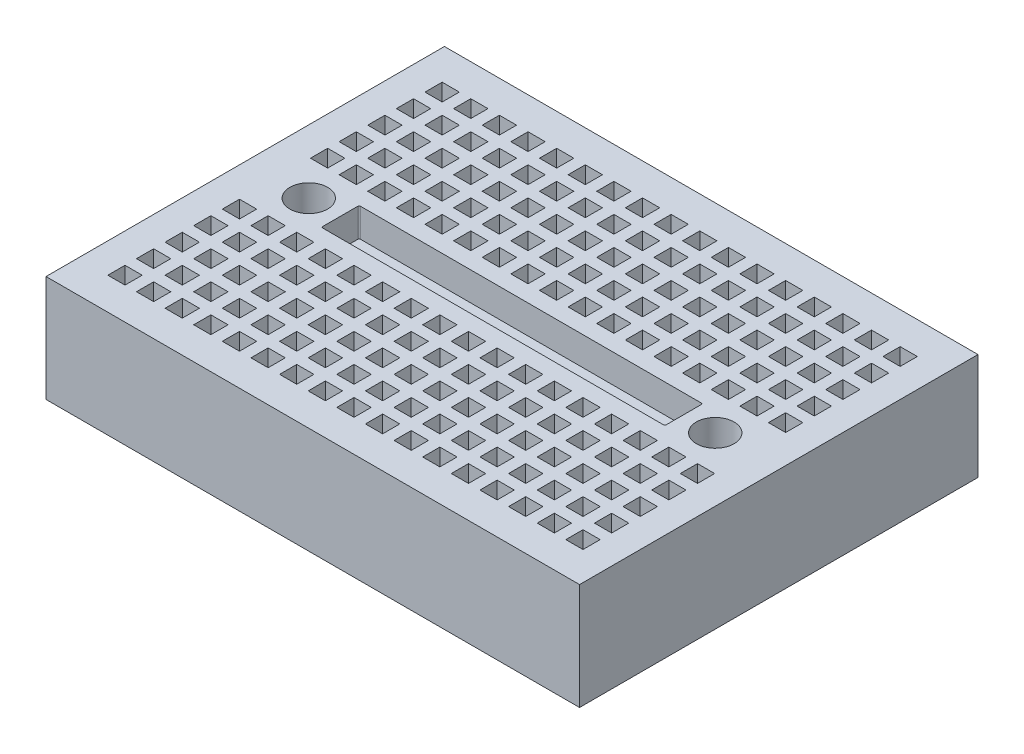
SolidWorks part; units mm, degrees
material "ABS"
ref_plane "Alzado" through (0, 0, 0) normal (0, 0, 1) x (1, 0, 0)
ref_plane "Planta" through (0, 0, 0) normal (0, 1, 0) x (1, 0, 0)
ref_plane "Vista lateral" through (0, 0, 0) normal (1, 0, 0) x (0, 0, -1)
sketch "Croquis2" plane through (0, 0, 0) normal (0, 1, 0) x (1, 0, 0)
  line L1 (-23.3, -17.4) -> (23.3, -17.4)
  line L2 (-23.3, -17.4) -> (-23.3, 17.4)
  line L3 (-23.3, 17.4) -> (23.3, 17.4)
  line L4 (23.3, -17.4) -> (23.3, 17.4)
  line L5 (-23.3, -17.4) -> (23.3, 17.4) construction
  line L6 (-23.3, 17.4) -> (23.3, -17.4) construction
  point P0 (0, 0)
  dimension "D1" = 34.8
  dimension "D2" = 46.6
extrude "Saliente-Extruir1" add sketch "Croquis2" along normal blind 9.3
sketch "Croquis3" plane through (0, 9.3, 0) normal (0, 1, 0) x (1, 0, 0)
  line L0 (23.3, -17.4) -> (23.3, 17.4) construction
  line L1 (20.8, -14.6) -> (19.3, -14.6)
  line L2 (20.8, -14.6) -> (20.8, -13.1)
  line L3 (20.8, -13.1) -> (19.3, -13.1)
  line L4 (19.3, -14.6) -> (19.3, -13.1)
  line L5 (-23.3, -17.4) -> (23.3, -17.4) construction
  line L6 (18.3, -14.6) -> (18.3, -13.1)
  line L7 (18.3, -14.6) -> (16.8, -14.6)
  line L8 (16.8, -14.6) -> (16.8, -13.1)
  line L9 (18.3, -13.1) -> (16.8, -13.1)
  line L10 (15.8, -14.6) -> (15.8, -13.1)
  line L11 (15.8, -14.6) -> (14.3, -14.6)
  line L12 (14.3, -14.6) -> (14.3, -13.1)
  line L13 (15.8, -13.1) -> (14.3, -13.1)
  line L14 (13.3, -14.6) -> (13.3, -13.1)
  line L15 (13.3, -14.6) -> (11.8, -14.6)
  line L16 (11.8, -14.6) -> (11.8, -13.1)
  line L17 (13.3, -13.1) -> (11.8, -13.1)
  line L18 (10.8, -14.6) -> (10.8, -13.1)
  line L19 (10.8, -14.6) -> (9.3, -14.6)
  line L20 (9.3, -14.6) -> (9.3, -13.1)
  line L21 (10.8, -13.1) -> (9.3, -13.1)
  line L22 (8.3, -14.6) -> (8.3, -13.1)
  line L23 (8.3, -14.6) -> (6.8, -14.6)
  line L24 (6.8, -14.6) -> (6.8, -13.1)
  line L25 (8.3, -13.1) -> (6.8, -13.1)
  line L26 (5.8, -14.6) -> (5.8, -13.1)
  line L27 (5.8, -14.6) -> (4.3, -14.6)
  line L28 (4.3, -14.6) -> (4.3, -13.1)
  line L29 (5.8, -13.1) -> (4.3, -13.1)
  line L30 (3.3, -14.6) -> (3.3, -13.1)
  line L31 (3.3, -14.6) -> (1.8, -14.6)
  line L32 (1.8, -14.6) -> (1.8, -13.1)
  line L33 (3.3, -13.1) -> (1.8, -13.1)
  line L34 (0.8, -14.6) -> (0.8, -13.1)
  line L35 (0.8, -14.6) -> (-0.7, -14.6)
  line L36 (-0.7, -14.6) -> (-0.7, -13.1)
  line L37 (0.8, -13.1) -> (-0.7, -13.1)
  line L38 (-1.7, -14.6) -> (-1.7, -13.1)
  line L39 (-1.7, -14.6) -> (-3.2, -14.6)
  line L40 (-3.2, -14.6) -> (-3.2, -13.1)
  line L41 (-1.7, -13.1) -> (-3.2, -13.1)
  line L42 (-4.2, -14.6) -> (-4.2, -13.1)
  line L43 (-4.2, -14.6) -> (-5.7, -14.6)
  line L44 (-5.7, -14.6) -> (-5.7, -13.1)
  line L45 (-4.2, -13.1) -> (-5.7, -13.1)
  line L46 (-6.7, -14.6) -> (-6.7, -13.1)
  line L47 (-6.7, -14.6) -> (-8.2, -14.6)
  line L48 (-8.2, -14.6) -> (-8.2, -13.1)
  line L49 (-6.7, -13.1) -> (-8.2, -13.1)
  line L50 (-9.2, -14.6) -> (-9.2, -13.1)
  line L51 (-9.2, -14.6) -> (-10.7, -14.6)
  line L52 (-10.7, -14.6) -> (-10.7, -13.1)
  line L53 (-9.2, -13.1) -> (-10.7, -13.1)
  line L54 (-11.7, -14.6) -> (-11.7, -13.1)
  line L55 (-11.7, -14.6) -> (-13.2, -14.6)
  line L56 (-13.2, -14.6) -> (-13.2, -13.1)
  line L57 (-11.7, -13.1) -> (-13.2, -13.1)
  line L58 (-14.2, -14.6) -> (-14.2, -13.1)
  line L59 (-14.2, -14.6) -> (-15.7, -14.6)
  line L60 (-15.7, -14.6) -> (-15.7, -13.1)
  line L61 (-14.2, -13.1) -> (-15.7, -13.1)
  line L62 (-16.7, -14.6) -> (-16.7, -13.1)
  line L63 (-16.7, -14.6) -> (-18.2, -14.6)
  line L64 (-18.2, -14.6) -> (-18.2, -13.1)
  line L65 (-16.7, -13.1) -> (-18.2, -13.1)
  line L66 (-19.2, -14.6) -> (-19.2, -13.1)
  line L67 (-19.2, -14.6) -> (-20.7, -14.6)
  line L68 (-20.7, -14.6) -> (-20.7, -13.1)
  line L69 (-19.2, -13.1) -> (-20.7, -13.1)
  line L70 (-19.2, -12.1) -> (-19.2, -10.6)
  line L71 (-19.2, -10.6) -> (-20.7, -10.6)
  line L72 (-20.7, -12.1) -> (-20.7, -10.6)
  line L73 (-19.2, -12.1) -> (-20.7, -12.1)
  line L74 (-16.7, -12.1) -> (-16.7, -10.6)
  line L75 (-16.7, -10.6) -> (-18.2, -10.6)
  line L76 (-18.2, -12.1) -> (-18.2, -10.6)
  line L77 (-16.7, -12.1) -> (-18.2, -12.1)
  line L78 (-14.2, -12.1) -> (-14.2, -10.6)
  line L79 (-14.2, -10.6) -> (-15.7, -10.6)
  line L80 (-15.7, -12.1) -> (-15.7, -10.6)
  line L81 (-14.2, -12.1) -> (-15.7, -12.1)
  line L82 (-11.7, -12.1) -> (-11.7, -10.6)
  line L83 (-11.7, -10.6) -> (-13.2, -10.6)
  line L84 (-13.2, -12.1) -> (-13.2, -10.6)
  line L85 (-11.7, -12.1) -> (-13.2, -12.1)
  line L86 (3.3, -12.1) -> (3.3, -10.6)
  line L87 (3.3, -10.6) -> (1.8, -10.6)
  line L88 (1.8, -12.1) -> (1.8, -10.6)
  line L89 (3.3, -12.1) -> (1.8, -12.1)
  line L90 (0.8, -12.1) -> (0.8, -10.6)
  line L91 (0.8, -10.6) -> (-0.7, -10.6)
  line L92 (-0.7, -12.1) -> (-0.7, -10.6)
  line L93 (0.8, -12.1) -> (-0.7, -12.1)
  line L94 (-1.7, -12.1) -> (-1.7, -10.6)
  line L95 (-1.7, -10.6) -> (-3.2, -10.6)
  line L96 (-3.2, -12.1) -> (-3.2, -10.6)
  line L97 (-1.7, -12.1) -> (-3.2, -12.1)
  line L98 (-4.2, -12.1) -> (-4.2, -10.6)
  line L99 (-4.2, -10.6) -> (-5.7, -10.6)
  line L100 (-5.7, -12.1) -> (-5.7, -10.6)
  line L101 (-4.2, -12.1) -> (-5.7, -12.1)
  line L102 (-9.2, -12.1) -> (-9.2, -10.6)
  line L103 (-9.2, -10.6) -> (-10.7, -10.6)
  line L104 (-10.7, -12.1) -> (-10.7, -10.6)
  line L105 (-9.2, -12.1) -> (-10.7, -12.1)
  line L106 (-6.7, -12.1) -> (-6.7, -10.6)
  line L107 (-6.7, -10.6) -> (-8.2, -10.6)
  line L108 (-8.2, -12.1) -> (-8.2, -10.6)
  line L109 (-6.7, -12.1) -> (-8.2, -12.1)
  line L110 (5.8, -12.1) -> (5.8, -10.6)
  line L111 (5.8, -10.6) -> (4.3, -10.6)
  line L112 (4.3, -12.1) -> (4.3, -10.6)
  line L113 (5.8, -12.1) -> (4.3, -12.1)
  line L114 (8.3, -12.1) -> (8.3, -10.6)
  line L115 (8.3, -10.6) -> (6.8, -10.6)
  line L116 (6.8, -12.1) -> (6.8, -10.6)
  line L117 (8.3, -12.1) -> (6.8, -12.1)
  line L118 (10.8, -12.1) -> (10.8, -10.6)
  line L119 (10.8, -10.6) -> (9.3, -10.6)
  line L120 (9.3, -12.1) -> (9.3, -10.6)
  line L121 (10.8, -12.1) -> (9.3, -12.1)
  line L122 (13.3, -12.1) -> (13.3, -10.6)
  line L123 (13.3, -10.6) -> (11.8, -10.6)
  line L124 (11.8, -12.1) -> (11.8, -10.6)
  line L125 (13.3, -12.1) -> (11.8, -12.1)
  line L126 (15.8, -12.1) -> (15.8, -10.6)
  line L127 (15.8, -10.6) -> (14.3, -10.6)
  line L128 (14.3, -12.1) -> (14.3, -10.6)
  line L129 (15.8, -12.1) -> (14.3, -12.1)
  line L130 (18.3, -12.1) -> (18.3, -10.6)
  line L131 (18.3, -10.6) -> (16.8, -10.6)
  line L132 (16.8, -12.1) -> (16.8, -10.6)
  line L133 (18.3, -12.1) -> (16.8, -12.1)
  line L134 (20.8, -12.1) -> (20.8, -10.6)
  line L135 (20.8, -12.1) -> (19.3, -12.1)
  line L136 (19.3, -12.1) -> (19.3, -10.6)
  line L137 (20.8, -10.6) -> (19.3, -10.6)
  line L138 (-19.2, -9.6) -> (-19.2, -8.1)
  line L139 (-19.2, -8.1) -> (-20.7, -8.1)
  line L140 (-20.7, -9.6) -> (-20.7, -8.1)
  line L141 (-19.2, -9.6) -> (-20.7, -9.6)
  line L142 (-16.7, -9.6) -> (-16.7, -8.1)
  line L143 (-16.7, -8.1) -> (-18.2, -8.1)
  line L144 (-18.2, -9.6) -> (-18.2, -8.1)
  line L145 (-16.7, -9.6) -> (-18.2, -9.6)
  line L146 (-14.2, -9.6) -> (-14.2, -8.1)
  line L147 (-14.2, -8.1) -> (-15.7, -8.1)
  line L148 (-15.7, -9.6) -> (-15.7, -8.1)
  line L149 (-14.2, -9.6) -> (-15.7, -9.6)
  line L150 (-11.7, -9.6) -> (-11.7, -8.1)
  line L151 (-11.7, -8.1) -> (-13.2, -8.1)
  line L152 (-13.2, -9.6) -> (-13.2, -8.1)
  line L153 (-11.7, -9.6) -> (-13.2, -9.6)
  line L154 (3.3, -9.6) -> (3.3, -8.1)
  line L155 (3.3, -8.1) -> (1.8, -8.1)
  line L156 (1.8, -9.6) -> (1.8, -8.1)
  line L157 (3.3, -9.6) -> (1.8, -9.6)
  line L158 (0.8, -9.6) -> (0.8, -8.1)
  line L159 (0.8, -8.1) -> (-0.7, -8.1)
  line L160 (-0.7, -9.6) -> (-0.7, -8.1)
  line L161 (0.8, -9.6) -> (-0.7, -9.6)
  line L162 (-1.7, -9.6) -> (-1.7, -8.1)
  line L163 (-1.7, -8.1) -> (-3.2, -8.1)
  line L164 (-3.2, -9.6) -> (-3.2, -8.1)
  line L165 (-1.7, -9.6) -> (-3.2, -9.6)
  line L166 (-4.2, -9.6) -> (-4.2, -8.1)
  line L167 (-4.2, -8.1) -> (-5.7, -8.1)
  line L168 (-5.7, -9.6) -> (-5.7, -8.1)
  line L169 (-4.2, -9.6) -> (-5.7, -9.6)
  line L170 (-9.2, -9.6) -> (-9.2, -8.1)
  line L171 (-9.2, -8.1) -> (-10.7, -8.1)
  line L172 (-10.7, -9.6) -> (-10.7, -8.1)
  line L173 (-9.2, -9.6) -> (-10.7, -9.6)
  line L174 (-6.7, -9.6) -> (-6.7, -8.1)
  line L175 (-6.7, -8.1) -> (-8.2, -8.1)
  line L176 (-8.2, -9.6) -> (-8.2, -8.1)
  line L177 (-6.7, -9.6) -> (-8.2, -9.6)
  line L178 (5.8, -9.6) -> (5.8, -8.1)
  line L179 (5.8, -8.1) -> (4.3, -8.1)
  line L180 (4.3, -9.6) -> (4.3, -8.1)
  line L181 (5.8, -9.6) -> (4.3, -9.6)
  line L182 (8.3, -9.6) -> (8.3, -8.1)
  line L183 (8.3, -8.1) -> (6.8, -8.1)
  line L184 (6.8, -9.6) -> (6.8, -8.1)
  line L185 (8.3, -9.6) -> (6.8, -9.6)
  line L186 (10.8, -9.6) -> (10.8, -8.1)
  line L187 (10.8, -8.1) -> (9.3, -8.1)
  line L188 (9.3, -9.6) -> (9.3, -8.1)
  line L189 (10.8, -9.6) -> (9.3, -9.6)
  line L190 (13.3, -9.6) -> (13.3, -8.1)
  line L191 (13.3, -8.1) -> (11.8, -8.1)
  line L192 (11.8, -9.6) -> (11.8, -8.1)
  line L193 (13.3, -9.6) -> (11.8, -9.6)
  line L194 (15.8, -9.6) -> (15.8, -8.1)
  line L195 (15.8, -8.1) -> (14.3, -8.1)
  line L196 (14.3, -9.6) -> (14.3, -8.1)
  line L197 (15.8, -9.6) -> (14.3, -9.6)
  line L198 (18.3, -9.6) -> (18.3, -8.1)
  line L199 (18.3, -8.1) -> (16.8, -8.1)
  line L200 (16.8, -9.6) -> (16.8, -8.1)
  line L201 (18.3, -9.6) -> (16.8, -9.6)
  line L202 (20.8, -9.6) -> (20.8, -8.1)
  line L203 (20.8, -9.6) -> (19.3, -9.6)
  line L204 (19.3, -9.6) -> (19.3, -8.1)
  line L205 (20.8, -8.1) -> (19.3, -8.1)
  line L206 (-19.2, -7.1) -> (-19.2, -5.6)
  line L207 (-19.2, -5.6) -> (-20.7, -5.6)
  line L208 (-20.7, -7.1) -> (-20.7, -5.6)
  line L209 (-19.2, -7.1) -> (-20.7, -7.1)
  line L210 (-16.7, -7.1) -> (-16.7, -5.6)
  line L211 (-16.7, -5.6) -> (-18.2, -5.6)
  line L212 (-18.2, -7.1) -> (-18.2, -5.6)
  line L213 (-16.7, -7.1) -> (-18.2, -7.1)
  line L214 (-14.2, -7.1) -> (-14.2, -5.6)
  line L215 (-14.2, -5.6) -> (-15.7, -5.6)
  line L216 (-15.7, -7.1) -> (-15.7, -5.6)
  line L217 (-14.2, -7.1) -> (-15.7, -7.1)
  line L218 (-11.7, -7.1) -> (-11.7, -5.6)
  line L219 (-11.7, -5.6) -> (-13.2, -5.6)
  line L220 (-13.2, -7.1) -> (-13.2, -5.6)
  line L221 (-11.7, -7.1) -> (-13.2, -7.1)
  line L222 (3.3, -7.1) -> (3.3, -5.6)
  line L223 (3.3, -5.6) -> (1.8, -5.6)
  line L224 (1.8, -7.1) -> (1.8, -5.6)
  line L225 (3.3, -7.1) -> (1.8, -7.1)
  line L226 (0.8, -7.1) -> (0.8, -5.6)
  line L227 (0.8, -5.6) -> (-0.7, -5.6)
  line L228 (-0.7, -7.1) -> (-0.7, -5.6)
  line L229 (0.8, -7.1) -> (-0.7, -7.1)
  line L230 (-1.7, -7.1) -> (-1.7, -5.6)
  line L231 (-1.7, -5.6) -> (-3.2, -5.6)
  line L232 (-3.2, -7.1) -> (-3.2, -5.6)
  line L233 (-1.7, -7.1) -> (-3.2, -7.1)
  line L234 (-4.2, -7.1) -> (-4.2, -5.6)
  line L235 (-4.2, -5.6) -> (-5.7, -5.6)
  line L236 (-5.7, -7.1) -> (-5.7, -5.6)
  line L237 (-4.2, -7.1) -> (-5.7, -7.1)
  line L238 (-9.2, -7.1) -> (-9.2, -5.6)
  line L239 (-9.2, -5.6) -> (-10.7, -5.6)
  line L240 (-10.7, -7.1) -> (-10.7, -5.6)
  line L241 (-9.2, -7.1) -> (-10.7, -7.1)
  line L242 (-6.7, -7.1) -> (-6.7, -5.6)
  line L243 (-6.7, -5.6) -> (-8.2, -5.6)
  line L244 (-8.2, -7.1) -> (-8.2, -5.6)
  line L245 (-6.7, -7.1) -> (-8.2, -7.1)
  line L246 (5.8, -7.1) -> (5.8, -5.6)
  line L247 (5.8, -5.6) -> (4.3, -5.6)
  line L248 (4.3, -7.1) -> (4.3, -5.6)
  line L249 (5.8, -7.1) -> (4.3, -7.1)
  line L250 (8.3, -7.1) -> (8.3, -5.6)
  line L251 (8.3, -5.6) -> (6.8, -5.6)
  line L252 (6.8, -7.1) -> (6.8, -5.6)
  line L253 (8.3, -7.1) -> (6.8, -7.1)
  line L254 (10.8, -7.1) -> (10.8, -5.6)
  line L255 (10.8, -5.6) -> (9.3, -5.6)
  line L256 (9.3, -7.1) -> (9.3, -5.6)
  line L257 (10.8, -7.1) -> (9.3, -7.1)
  line L258 (13.3, -7.1) -> (13.3, -5.6)
  line L259 (13.3, -5.6) -> (11.8, -5.6)
  line L260 (11.8, -7.1) -> (11.8, -5.6)
  line L261 (13.3, -7.1) -> (11.8, -7.1)
  line L262 (15.8, -7.1) -> (15.8, -5.6)
  line L263 (15.8, -5.6) -> (14.3, -5.6)
  line L264 (14.3, -7.1) -> (14.3, -5.6)
  line L265 (15.8, -7.1) -> (14.3, -7.1)
  line L266 (18.3, -7.1) -> (18.3, -5.6)
  line L267 (18.3, -5.6) -> (16.8, -5.6)
  line L268 (16.8, -7.1) -> (16.8, -5.6)
  line L269 (18.3, -7.1) -> (16.8, -7.1)
  line L270 (20.8, -7.1) -> (20.8, -5.6)
  line L271 (20.8, -7.1) -> (19.3, -7.1)
  line L272 (19.3, -7.1) -> (19.3, -5.6)
  line L273 (20.8, -5.6) -> (19.3, -5.6)
  line L274 (-19.2, -4.6) -> (-19.2, -3.1)
  line L275 (-19.2, -3.1) -> (-20.7, -3.1)
  line L276 (-20.7, -4.6) -> (-20.7, -3.1)
  line L277 (-19.2, -4.6) -> (-20.7, -4.6)
  line L278 (-16.7, -4.6) -> (-16.7, -3.1)
  line L279 (-16.7, -3.1) -> (-18.2, -3.1)
  line L280 (-18.2, -4.6) -> (-18.2, -3.1)
  line L281 (-16.7, -4.6) -> (-18.2, -4.6)
  line L282 (-14.2, -4.6) -> (-14.2, -3.1)
  line L283 (-14.2, -3.1) -> (-15.7, -3.1)
  line L284 (-15.7, -4.6) -> (-15.7, -3.1)
  line L285 (-14.2, -4.6) -> (-15.7, -4.6)
  line L286 (-11.7, -4.6) -> (-11.7, -3.1)
  line L287 (-11.7, -3.1) -> (-13.2, -3.1)
  line L288 (-13.2, -4.6) -> (-13.2, -3.1)
  line L289 (-11.7, -4.6) -> (-13.2, -4.6)
  line L290 (3.3, -4.6) -> (3.3, -3.1)
  line L291 (3.3, -3.1) -> (1.8, -3.1)
  line L292 (1.8, -4.6) -> (1.8, -3.1)
  line L293 (3.3, -4.6) -> (1.8, -4.6)
  line L294 (0.8, -4.6) -> (0.8, -3.1)
  line L295 (0.8, -3.1) -> (-0.7, -3.1)
  line L296 (-0.7, -4.6) -> (-0.7, -3.1)
  line L297 (0.8, -4.6) -> (-0.7, -4.6)
  line L298 (-1.7, -4.6) -> (-1.7, -3.1)
  line L299 (-1.7, -3.1) -> (-3.2, -3.1)
  line L300 (-3.2, -4.6) -> (-3.2, -3.1)
  line L301 (-1.7, -4.6) -> (-3.2, -4.6)
  line L302 (-4.2, -4.6) -> (-4.2, -3.1)
  line L303 (-4.2, -3.1) -> (-5.7, -3.1)
  line L304 (-5.7, -4.6) -> (-5.7, -3.1)
  line L305 (-4.2, -4.6) -> (-5.7, -4.6)
  line L306 (-9.2, -4.6) -> (-9.2, -3.1)
  line L307 (-9.2, -3.1) -> (-10.7, -3.1)
  line L308 (-10.7, -4.6) -> (-10.7, -3.1)
  line L309 (-9.2, -4.6) -> (-10.7, -4.6)
  line L310 (-6.7, -4.6) -> (-6.7, -3.1)
  line L311 (-6.7, -3.1) -> (-8.2, -3.1)
  line L312 (-8.2, -4.6) -> (-8.2, -3.1)
  line L313 (-6.7, -4.6) -> (-8.2, -4.6)
  line L314 (5.8, -4.6) -> (5.8, -3.1)
  line L315 (5.8, -3.1) -> (4.3, -3.1)
  line L316 (4.3, -4.6) -> (4.3, -3.1)
  line L317 (5.8, -4.6) -> (4.3, -4.6)
  line L318 (8.3, -4.6) -> (8.3, -3.1)
  line L319 (8.3, -3.1) -> (6.8, -3.1)
  line L320 (6.8, -4.6) -> (6.8, -3.1)
  line L321 (8.3, -4.6) -> (6.8, -4.6)
  line L322 (10.8, -4.6) -> (10.8, -3.1)
  line L323 (10.8, -3.1) -> (9.3, -3.1)
  line L324 (9.3, -4.6) -> (9.3, -3.1)
  line L325 (10.8, -4.6) -> (9.3, -4.6)
  line L326 (13.3, -4.6) -> (13.3, -3.1)
  line L327 (13.3, -3.1) -> (11.8, -3.1)
  line L328 (11.8, -4.6) -> (11.8, -3.1)
  line L329 (13.3, -4.6) -> (11.8, -4.6)
  line L330 (15.8, -4.6) -> (15.8, -3.1)
  line L331 (15.8, -3.1) -> (14.3, -3.1)
  line L332 (14.3, -4.6) -> (14.3, -3.1)
  line L333 (15.8, -4.6) -> (14.3, -4.6)
  line L334 (18.3, -4.6) -> (18.3, -3.1)
  line L335 (18.3, -3.1) -> (16.8, -3.1)
  line L336 (16.8, -4.6) -> (16.8, -3.1)
  line L337 (18.3, -4.6) -> (16.8, -4.6)
  line L338 (20.8, -4.6) -> (20.8, -3.1)
  line L339 (20.8, -4.6) -> (19.3, -4.6)
  line L340 (19.3, -4.6) -> (19.3, -3.1)
  line L341 (20.8, -3.1) -> (19.3, -3.1)
  line L342 (-19.2, -14.6) -> (-19.2, -12.1) construction
  line L343 (-23.3, 0) -> (23.3, 0) construction
  line L344 (-23.3, 17.4) -> (-23.3, -17.4) construction
  line L345 (-19.2, 14.6) -> (-19.2, 12.1) construction
  line L346 (20.8, 3.1) -> (19.3, 3.1)
  line L347 (19.3, 4.6) -> (19.3, 3.1)
  line L348 (20.8, 4.6) -> (19.3, 4.6)
  line L349 (20.8, 4.6) -> (20.8, 3.1)
  line L350 (18.3, 4.6) -> (16.8, 4.6)
  line L351 (16.8, 4.6) -> (16.8, 3.1)
  line L352 (18.3, 3.1) -> (16.8, 3.1)
  line L353 (18.3, 4.6) -> (18.3, 3.1)
  line L354 (15.8, 4.6) -> (14.3, 4.6)
  line L355 (14.3, 4.6) -> (14.3, 3.1)
  line L356 (15.8, 3.1) -> (14.3, 3.1)
  line L357 (15.8, 4.6) -> (15.8, 3.1)
  line L358 (13.3, 4.6) -> (11.8, 4.6)
  line L359 (11.8, 4.6) -> (11.8, 3.1)
  line L360 (13.3, 3.1) -> (11.8, 3.1)
  line L361 (13.3, 4.6) -> (13.3, 3.1)
  line L362 (10.8, 4.6) -> (9.3, 4.6)
  line L363 (9.3, 4.6) -> (9.3, 3.1)
  line L364 (10.8, 3.1) -> (9.3, 3.1)
  line L365 (10.8, 4.6) -> (10.8, 3.1)
  line L366 (8.3, 4.6) -> (6.8, 4.6)
  line L367 (6.8, 4.6) -> (6.8, 3.1)
  line L368 (8.3, 3.1) -> (6.8, 3.1)
  line L369 (8.3, 4.6) -> (8.3, 3.1)
  line L370 (5.8, 4.6) -> (4.3, 4.6)
  line L371 (4.3, 4.6) -> (4.3, 3.1)
  line L372 (5.8, 3.1) -> (4.3, 3.1)
  line L373 (5.8, 4.6) -> (5.8, 3.1)
  line L374 (-6.7, 4.6) -> (-8.2, 4.6)
  line L375 (-8.2, 4.6) -> (-8.2, 3.1)
  line L376 (-6.7, 3.1) -> (-8.2, 3.1)
  line L377 (-6.7, 4.6) -> (-6.7, 3.1)
  line L378 (-9.2, 4.6) -> (-10.7, 4.6)
  line L379 (-10.7, 4.6) -> (-10.7, 3.1)
  line L380 (-9.2, 3.1) -> (-10.7, 3.1)
  line L381 (-9.2, 4.6) -> (-9.2, 3.1)
  line L382 (-4.2, 4.6) -> (-5.7, 4.6)
  line L383 (-5.7, 4.6) -> (-5.7, 3.1)
  line L384 (-4.2, 3.1) -> (-5.7, 3.1)
  line L385 (-4.2, 4.6) -> (-4.2, 3.1)
  line L386 (-1.7, 4.6) -> (-3.2, 4.6)
  line L387 (-3.2, 4.6) -> (-3.2, 3.1)
  line L388 (-1.7, 3.1) -> (-3.2, 3.1)
  line L389 (-1.7, 4.6) -> (-1.7, 3.1)
  line L390 (0.8, 4.6) -> (-0.7, 4.6)
  line L391 (-0.7, 4.6) -> (-0.7, 3.1)
  line L392 (0.8, 3.1) -> (-0.7, 3.1)
  line L393 (0.8, 4.6) -> (0.8, 3.1)
  line L394 (3.3, 4.6) -> (1.8, 4.6)
  line L395 (1.8, 4.6) -> (1.8, 3.1)
  line L396 (3.3, 3.1) -> (1.8, 3.1)
  line L397 (3.3, 4.6) -> (3.3, 3.1)
  line L398 (-11.7, 4.6) -> (-13.2, 4.6)
  line L399 (-13.2, 4.6) -> (-13.2, 3.1)
  line L400 (-11.7, 3.1) -> (-13.2, 3.1)
  line L401 (-11.7, 4.6) -> (-11.7, 3.1)
  line L402 (-14.2, 4.6) -> (-15.7, 4.6)
  line L403 (-15.7, 4.6) -> (-15.7, 3.1)
  line L404 (-14.2, 3.1) -> (-15.7, 3.1)
  line L405 (-14.2, 4.6) -> (-14.2, 3.1)
  line L406 (-16.7, 4.6) -> (-18.2, 4.6)
  line L407 (-18.2, 4.6) -> (-18.2, 3.1)
  line L408 (-16.7, 3.1) -> (-18.2, 3.1)
  line L409 (-16.7, 4.6) -> (-16.7, 3.1)
  line L410 (-19.2, 4.6) -> (-20.7, 4.6)
  line L411 (-20.7, 4.6) -> (-20.7, 3.1)
  line L412 (-19.2, 3.1) -> (-20.7, 3.1)
  line L413 (-19.2, 4.6) -> (-19.2, 3.1)
  line L414 (20.8, 5.6) -> (19.3, 5.6)
  line L415 (19.3, 7.1) -> (19.3, 5.6)
  line L416 (20.8, 7.1) -> (19.3, 7.1)
  line L417 (20.8, 7.1) -> (20.8, 5.6)
  line L418 (18.3, 7.1) -> (16.8, 7.1)
  line L419 (16.8, 7.1) -> (16.8, 5.6)
  line L420 (18.3, 5.6) -> (16.8, 5.6)
  line L421 (18.3, 7.1) -> (18.3, 5.6)
  line L422 (15.8, 7.1) -> (14.3, 7.1)
  line L423 (14.3, 7.1) -> (14.3, 5.6)
  line L424 (15.8, 5.6) -> (14.3, 5.6)
  line L425 (15.8, 7.1) -> (15.8, 5.6)
  line L426 (13.3, 7.1) -> (11.8, 7.1)
  line L427 (11.8, 7.1) -> (11.8, 5.6)
  line L428 (13.3, 5.6) -> (11.8, 5.6)
  line L429 (13.3, 7.1) -> (13.3, 5.6)
  line L430 (10.8, 7.1) -> (9.3, 7.1)
  line L431 (9.3, 7.1) -> (9.3, 5.6)
  line L432 (10.8, 5.6) -> (9.3, 5.6)
  line L433 (10.8, 7.1) -> (10.8, 5.6)
  line L434 (8.3, 7.1) -> (6.8, 7.1)
  line L435 (6.8, 7.1) -> (6.8, 5.6)
  line L436 (8.3, 5.6) -> (6.8, 5.6)
  line L437 (8.3, 7.1) -> (8.3, 5.6)
  line L438 (5.8, 7.1) -> (4.3, 7.1)
  line L439 (4.3, 7.1) -> (4.3, 5.6)
  line L440 (5.8, 5.6) -> (4.3, 5.6)
  line L441 (5.8, 7.1) -> (5.8, 5.6)
  line L442 (-6.7, 7.1) -> (-8.2, 7.1)
  line L443 (-8.2, 7.1) -> (-8.2, 5.6)
  line L444 (-6.7, 5.6) -> (-8.2, 5.6)
  line L445 (-6.7, 7.1) -> (-6.7, 5.6)
  line L446 (-9.2, 7.1) -> (-10.7, 7.1)
  line L447 (-10.7, 7.1) -> (-10.7, 5.6)
  line L448 (-9.2, 5.6) -> (-10.7, 5.6)
  line L449 (-9.2, 7.1) -> (-9.2, 5.6)
  line L450 (-4.2, 7.1) -> (-5.7, 7.1)
  line L451 (-5.7, 7.1) -> (-5.7, 5.6)
  line L452 (-4.2, 5.6) -> (-5.7, 5.6)
  line L453 (-4.2, 7.1) -> (-4.2, 5.6)
  line L454 (-1.7, 7.1) -> (-3.2, 7.1)
  line L455 (-3.2, 7.1) -> (-3.2, 5.6)
  line L456 (-1.7, 5.6) -> (-3.2, 5.6)
  line L457 (-1.7, 7.1) -> (-1.7, 5.6)
  line L458 (0.8, 7.1) -> (-0.7, 7.1)
  line L459 (-0.7, 7.1) -> (-0.7, 5.6)
  line L460 (0.8, 5.6) -> (-0.7, 5.6)
  line L461 (0.8, 7.1) -> (0.8, 5.6)
  line L462 (3.3, 7.1) -> (1.8, 7.1)
  line L463 (1.8, 7.1) -> (1.8, 5.6)
  line L464 (3.3, 5.6) -> (1.8, 5.6)
  line L465 (3.3, 7.1) -> (3.3, 5.6)
  line L466 (-11.7, 7.1) -> (-13.2, 7.1)
  line L467 (-13.2, 7.1) -> (-13.2, 5.6)
  line L468 (-11.7, 5.6) -> (-13.2, 5.6)
  line L469 (-11.7, 7.1) -> (-11.7, 5.6)
  line L470 (-14.2, 7.1) -> (-15.7, 7.1)
  line L471 (-15.7, 7.1) -> (-15.7, 5.6)
  line L472 (-14.2, 5.6) -> (-15.7, 5.6)
  line L473 (-14.2, 7.1) -> (-14.2, 5.6)
  line L474 (-16.7, 7.1) -> (-18.2, 7.1)
  line L475 (-18.2, 7.1) -> (-18.2, 5.6)
  line L476 (-16.7, 5.6) -> (-18.2, 5.6)
  line L477 (-16.7, 7.1) -> (-16.7, 5.6)
  line L478 (-19.2, 7.1) -> (-20.7, 7.1)
  line L479 (-20.7, 7.1) -> (-20.7, 5.6)
  line L480 (-19.2, 5.6) -> (-20.7, 5.6)
  line L481 (-19.2, 7.1) -> (-19.2, 5.6)
  line L482 (20.8, 8.1) -> (19.3, 8.1)
  line L483 (19.3, 9.6) -> (19.3, 8.1)
  line L484 (20.8, 9.6) -> (19.3, 9.6)
  line L485 (20.8, 9.6) -> (20.8, 8.1)
  line L486 (18.3, 9.6) -> (16.8, 9.6)
  line L487 (16.8, 9.6) -> (16.8, 8.1)
  line L488 (18.3, 8.1) -> (16.8, 8.1)
  line L489 (18.3, 9.6) -> (18.3, 8.1)
  line L490 (15.8, 9.6) -> (14.3, 9.6)
  line L491 (14.3, 9.6) -> (14.3, 8.1)
  line L492 (15.8, 8.1) -> (14.3, 8.1)
  line L493 (15.8, 9.6) -> (15.8, 8.1)
  line L494 (13.3, 9.6) -> (11.8, 9.6)
  line L495 (11.8, 9.6) -> (11.8, 8.1)
  line L496 (13.3, 8.1) -> (11.8, 8.1)
  line L497 (13.3, 9.6) -> (13.3, 8.1)
  line L498 (10.8, 9.6) -> (9.3, 9.6)
  line L499 (9.3, 9.6) -> (9.3, 8.1)
  line L500 (10.8, 8.1) -> (9.3, 8.1)
  line L501 (10.8, 9.6) -> (10.8, 8.1)
  line L502 (8.3, 9.6) -> (6.8, 9.6)
  line L503 (6.8, 9.6) -> (6.8, 8.1)
  line L504 (8.3, 8.1) -> (6.8, 8.1)
  line L505 (8.3, 9.6) -> (8.3, 8.1)
  line L506 (5.8, 9.6) -> (4.3, 9.6)
  line L507 (4.3, 9.6) -> (4.3, 8.1)
  line L508 (5.8, 8.1) -> (4.3, 8.1)
  line L509 (5.8, 9.6) -> (5.8, 8.1)
  line L510 (-6.7, 9.6) -> (-8.2, 9.6)
  line L511 (-8.2, 9.6) -> (-8.2, 8.1)
  line L512 (-6.7, 8.1) -> (-8.2, 8.1)
  line L513 (-6.7, 9.6) -> (-6.7, 8.1)
  line L514 (-9.2, 9.6) -> (-10.7, 9.6)
  line L515 (-10.7, 9.6) -> (-10.7, 8.1)
  line L516 (-9.2, 8.1) -> (-10.7, 8.1)
  line L517 (-9.2, 9.6) -> (-9.2, 8.1)
  line L518 (-4.2, 9.6) -> (-5.7, 9.6)
  line L519 (-5.7, 9.6) -> (-5.7, 8.1)
  line L520 (-4.2, 8.1) -> (-5.7, 8.1)
  line L521 (-4.2, 9.6) -> (-4.2, 8.1)
  line L522 (-1.7, 9.6) -> (-3.2, 9.6)
  line L523 (-3.2, 9.6) -> (-3.2, 8.1)
  line L524 (-1.7, 8.1) -> (-3.2, 8.1)
  line L525 (-1.7, 9.6) -> (-1.7, 8.1)
  line L526 (0.8, 9.6) -> (-0.7, 9.6)
  line L527 (-0.7, 9.6) -> (-0.7, 8.1)
  line L528 (0.8, 8.1) -> (-0.7, 8.1)
  line L529 (0.8, 9.6) -> (0.8, 8.1)
  line L530 (3.3, 9.6) -> (1.8, 9.6)
  line L531 (1.8, 9.6) -> (1.8, 8.1)
  line L532 (3.3, 8.1) -> (1.8, 8.1)
  line L533 (3.3, 9.6) -> (3.3, 8.1)
  line L534 (-11.7, 9.6) -> (-13.2, 9.6)
  line L535 (-13.2, 9.6) -> (-13.2, 8.1)
  line L536 (-11.7, 8.1) -> (-13.2, 8.1)
  line L537 (-11.7, 9.6) -> (-11.7, 8.1)
  line L538 (-14.2, 9.6) -> (-15.7, 9.6)
  line L539 (-15.7, 9.6) -> (-15.7, 8.1)
  line L540 (-14.2, 8.1) -> (-15.7, 8.1)
  line L541 (-14.2, 9.6) -> (-14.2, 8.1)
  line L542 (-16.7, 9.6) -> (-18.2, 9.6)
  line L543 (-18.2, 9.6) -> (-18.2, 8.1)
  line L544 (-16.7, 8.1) -> (-18.2, 8.1)
  line L545 (-16.7, 9.6) -> (-16.7, 8.1)
  line L546 (-19.2, 9.6) -> (-20.7, 9.6)
  line L547 (-20.7, 9.6) -> (-20.7, 8.1)
  line L548 (-19.2, 8.1) -> (-20.7, 8.1)
  line L549 (-19.2, 9.6) -> (-19.2, 8.1)
  line L550 (20.8, 10.6) -> (19.3, 10.6)
  line L551 (19.3, 12.1) -> (19.3, 10.6)
  line L552 (20.8, 12.1) -> (19.3, 12.1)
  line L553 (20.8, 12.1) -> (20.8, 10.6)
  line L554 (18.3, 12.1) -> (16.8, 12.1)
  line L555 (16.8, 12.1) -> (16.8, 10.6)
  line L556 (18.3, 10.6) -> (16.8, 10.6)
  line L557 (18.3, 12.1) -> (18.3, 10.6)
  line L558 (15.8, 12.1) -> (14.3, 12.1)
  line L559 (14.3, 12.1) -> (14.3, 10.6)
  line L560 (15.8, 10.6) -> (14.3, 10.6)
  line L561 (15.8, 12.1) -> (15.8, 10.6)
  line L562 (13.3, 12.1) -> (11.8, 12.1)
  line L563 (11.8, 12.1) -> (11.8, 10.6)
  line L564 (13.3, 10.6) -> (11.8, 10.6)
  line L565 (13.3, 12.1) -> (13.3, 10.6)
  line L566 (10.8, 12.1) -> (9.3, 12.1)
  line L567 (9.3, 12.1) -> (9.3, 10.6)
  line L568 (10.8, 10.6) -> (9.3, 10.6)
  line L569 (10.8, 12.1) -> (10.8, 10.6)
  line L570 (8.3, 12.1) -> (6.8, 12.1)
  line L571 (6.8, 12.1) -> (6.8, 10.6)
  line L572 (8.3, 10.6) -> (6.8, 10.6)
  line L573 (8.3, 12.1) -> (8.3, 10.6)
  line L574 (5.8, 12.1) -> (4.3, 12.1)
  line L575 (4.3, 12.1) -> (4.3, 10.6)
  line L576 (5.8, 10.6) -> (4.3, 10.6)
  line L577 (5.8, 12.1) -> (5.8, 10.6)
  line L578 (-6.7, 12.1) -> (-8.2, 12.1)
  line L579 (-8.2, 12.1) -> (-8.2, 10.6)
  line L580 (-6.7, 10.6) -> (-8.2, 10.6)
  line L581 (-6.7, 12.1) -> (-6.7, 10.6)
  line L582 (-9.2, 12.1) -> (-10.7, 12.1)
  line L583 (-10.7, 12.1) -> (-10.7, 10.6)
  line L584 (-9.2, 10.6) -> (-10.7, 10.6)
  line L585 (-9.2, 12.1) -> (-9.2, 10.6)
  line L586 (-4.2, 12.1) -> (-5.7, 12.1)
  line L587 (-5.7, 12.1) -> (-5.7, 10.6)
  line L588 (-4.2, 10.6) -> (-5.7, 10.6)
  line L589 (-4.2, 12.1) -> (-4.2, 10.6)
  line L590 (-1.7, 12.1) -> (-3.2, 12.1)
  line L591 (-3.2, 12.1) -> (-3.2, 10.6)
  line L592 (-1.7, 10.6) -> (-3.2, 10.6)
  line L593 (-1.7, 12.1) -> (-1.7, 10.6)
  line L594 (0.8, 12.1) -> (-0.7, 12.1)
  line L595 (-0.7, 12.1) -> (-0.7, 10.6)
  line L596 (0.8, 10.6) -> (-0.7, 10.6)
  line L597 (0.8, 12.1) -> (0.8, 10.6)
  line L598 (3.3, 12.1) -> (1.8, 12.1)
  line L599 (1.8, 12.1) -> (1.8, 10.6)
  line L600 (3.3, 10.6) -> (1.8, 10.6)
  line L601 (3.3, 12.1) -> (3.3, 10.6)
  line L602 (-11.7, 12.1) -> (-13.2, 12.1)
  line L603 (-13.2, 12.1) -> (-13.2, 10.6)
  line L604 (-11.7, 10.6) -> (-13.2, 10.6)
  line L605 (-11.7, 12.1) -> (-11.7, 10.6)
  line L606 (-14.2, 12.1) -> (-15.7, 12.1)
  line L607 (-15.7, 12.1) -> (-15.7, 10.6)
  line L608 (-14.2, 10.6) -> (-15.7, 10.6)
  line L609 (-14.2, 12.1) -> (-14.2, 10.6)
  line L610 (-16.7, 12.1) -> (-18.2, 12.1)
  line L611 (-18.2, 12.1) -> (-18.2, 10.6)
  line L612 (-16.7, 10.6) -> (-18.2, 10.6)
  line L613 (-16.7, 12.1) -> (-16.7, 10.6)
  line L614 (-19.2, 12.1) -> (-20.7, 12.1)
  line L615 (-20.7, 12.1) -> (-20.7, 10.6)
  line L616 (-19.2, 10.6) -> (-20.7, 10.6)
  line L617 (-19.2, 12.1) -> (-19.2, 10.6)
  line L618 (-19.2, 13.1) -> (-20.7, 13.1)
  line L619 (-20.7, 14.6) -> (-20.7, 13.1)
  line L620 (-19.2, 14.6) -> (-20.7, 14.6)
  line L621 (-19.2, 14.6) -> (-19.2, 13.1)
  line L622 (-16.7, 13.1) -> (-18.2, 13.1)
  line L623 (-18.2, 14.6) -> (-18.2, 13.1)
  line L624 (-16.7, 14.6) -> (-18.2, 14.6)
  line L625 (-16.7, 14.6) -> (-16.7, 13.1)
  line L626 (-14.2, 13.1) -> (-15.7, 13.1)
  line L627 (-15.7, 14.6) -> (-15.7, 13.1)
  line L628 (-14.2, 14.6) -> (-15.7, 14.6)
  line L629 (-14.2, 14.6) -> (-14.2, 13.1)
  line L630 (-11.7, 13.1) -> (-13.2, 13.1)
  line L631 (-13.2, 14.6) -> (-13.2, 13.1)
  line L632 (-11.7, 14.6) -> (-13.2, 14.6)
  line L633 (-11.7, 14.6) -> (-11.7, 13.1)
  line L634 (-9.2, 13.1) -> (-10.7, 13.1)
  line L635 (-10.7, 14.6) -> (-10.7, 13.1)
  line L636 (-9.2, 14.6) -> (-10.7, 14.6)
  line L637 (-9.2, 14.6) -> (-9.2, 13.1)
  line L638 (-6.7, 13.1) -> (-8.2, 13.1)
  line L639 (-8.2, 14.6) -> (-8.2, 13.1)
  line L640 (-6.7, 14.6) -> (-8.2, 14.6)
  line L641 (-6.7, 14.6) -> (-6.7, 13.1)
  line L642 (-4.2, 13.1) -> (-5.7, 13.1)
  line L643 (-5.7, 14.6) -> (-5.7, 13.1)
  line L644 (-4.2, 14.6) -> (-5.7, 14.6)
  line L645 (-4.2, 14.6) -> (-4.2, 13.1)
  line L646 (-1.7, 13.1) -> (-3.2, 13.1)
  line L647 (-3.2, 14.6) -> (-3.2, 13.1)
  line L648 (-1.7, 14.6) -> (-3.2, 14.6)
  line L649 (-1.7, 14.6) -> (-1.7, 13.1)
  line L650 (0.8, 13.1) -> (-0.7, 13.1)
  line L651 (-0.7, 14.6) -> (-0.7, 13.1)
  line L652 (0.8, 14.6) -> (-0.7, 14.6)
  line L653 (0.8, 14.6) -> (0.8, 13.1)
  line L654 (3.3, 13.1) -> (1.8, 13.1)
  line L655 (1.8, 14.6) -> (1.8, 13.1)
  line L656 (3.3, 14.6) -> (1.8, 14.6)
  line L657 (3.3, 14.6) -> (3.3, 13.1)
  line L658 (5.8, 13.1) -> (4.3, 13.1)
  line L659 (4.3, 14.6) -> (4.3, 13.1)
  line L660 (5.8, 14.6) -> (4.3, 14.6)
  line L661 (5.8, 14.6) -> (5.8, 13.1)
  line L662 (8.3, 13.1) -> (6.8, 13.1)
  line L663 (6.8, 14.6) -> (6.8, 13.1)
  line L664 (8.3, 14.6) -> (6.8, 14.6)
  line L665 (8.3, 14.6) -> (8.3, 13.1)
  line L666 (10.8, 13.1) -> (9.3, 13.1)
  line L667 (9.3, 14.6) -> (9.3, 13.1)
  line L668 (10.8, 14.6) -> (9.3, 14.6)
  line L669 (10.8, 14.6) -> (10.8, 13.1)
  line L670 (13.3, 13.1) -> (11.8, 13.1)
  line L671 (11.8, 14.6) -> (11.8, 13.1)
  line L672 (13.3, 14.6) -> (11.8, 14.6)
  line L673 (13.3, 14.6) -> (13.3, 13.1)
  line L674 (15.8, 13.1) -> (14.3, 13.1)
  line L675 (14.3, 14.6) -> (14.3, 13.1)
  line L676 (15.8, 14.6) -> (14.3, 14.6)
  line L677 (15.8, 14.6) -> (15.8, 13.1)
  line L678 (18.3, 13.1) -> (16.8, 13.1)
  line L679 (16.8, 14.6) -> (16.8, 13.1)
  line L680 (18.3, 14.6) -> (16.8, 14.6)
  line L681 (18.3, 14.6) -> (18.3, 13.1)
  line L682 (19.3, 14.6) -> (19.3, 13.1)
  line L683 (20.8, 13.1) -> (19.3, 13.1)
  line L684 (20.8, 14.6) -> (20.8, 13.1)
  line L685 (20.8, 14.6) -> (19.3, 14.6)
  dimension "D1" = 1.5
  dimension "D2" = 2.5
  dimension "D3" = 2.8
  dimension "D5" = 1
  dimension "D7" = 2.5
  dimension "D4" = 17
  dimension "D6" = 5
extrude "Cortar-Extruir1" cut sketch "Croquis3" against normal blind 6
sketch "Croquis4" plane through (0, 9.3, 0) normal (0, 1, 0) x (1, 0, 0)
  line L1 (-14.9, -1.65) -> (14.9, -1.65)
  line L2 (-15, -1.55) -> (-15, 1.55)
  line L3 (-14.9, 1.65) -> (14.9, 1.65)
  line L4 (15, -1.55) -> (15, 1.55)
  line L5 (-15, -1.65) -> (15, 1.65) construction
  line L6 (-15, 1.65) -> (15, -1.65) construction
  arc A0 (14.9, -1.65) -> (15, -1.55) centre (14.9, -1.55) ccw
  arc A1 (14.9, 1.65) -> (15, 1.55) centre (14.9, 1.55) cw
  arc A2 (-14.9, -1.65) -> (-15, -1.55) centre (-14.9, -1.55) cw
  arc A3 (-15, 1.55) -> (-14.9, 1.65) centre (-14.9, 1.55) cw
  point P0 (0, 0)
  dimension "D3" = 0.1
  dimension "D1" = 30
  dimension "D2" = 3.3
extrude "Cortar-Extruir2" cut sketch "Croquis4" against normal blind 2.5
sketch "Croquis5" plane through (0, 9.3, 0) normal (0, 1, 0) x (1, 0, 0)
  line L0 (15, -1.55) -> (15, 1.55) construction
  line L1 (14.9, 1.65) -> (-14.9, 1.65) construction
  circle A0 centre (17.75, 0) radius 1.65
  point P2 (16.1, 0)
  dimension "D1" = 1.1
extrude "Cortar-Extruir3" cut sketch "Croquis5" against normal up to surface (2.5 mm away) up to face at (0, 6.8, 0)
mirror "Simetría2" about plane through (0, 0, 0) normal (1, 0, 0) of "Cortar-Extruir3"
sketch "Croquis6" plane through (-23.3, 0, 0) normal (-1, 0, 0) x (0, 0, 1)
  line L0 (-17.4, 0) -> (17.4, 0) construction
  line L1 (-2, 0) -> (2, 0)
  line L2 (-2, 0) -> (-2, 5)
  line L3 (-2, 5) -> (2, 5)
  line L4 (2, 0) -> (2, 5)
  point P6 (0, 5)
  dimension "D1" = 5
  dimension "D2" = 4
extrude "Saliente-Extruir2" add sketch "Croquis6" along normal blind 1
sketch "Croquis7" plane through (0, 0, -17.4) normal (0, 0, -1) x (-1, 0, 0)
  line L0 (-23.3, 0) -> (23.3, 0) construction
  line L1 (-2, 0) -> (2, 0)
  line L2 (-2, 0) -> (-2, 5)
  line L3 (-2, 5) -> (2, 5)
  line L4 (2, 0) -> (2, 5)
  point P6 (0, 5)
  dimension "D1" = 4
  dimension "D2" = 5
extrude "Saliente-Extruir3" add sketch "Croquis7" along normal blind 1
